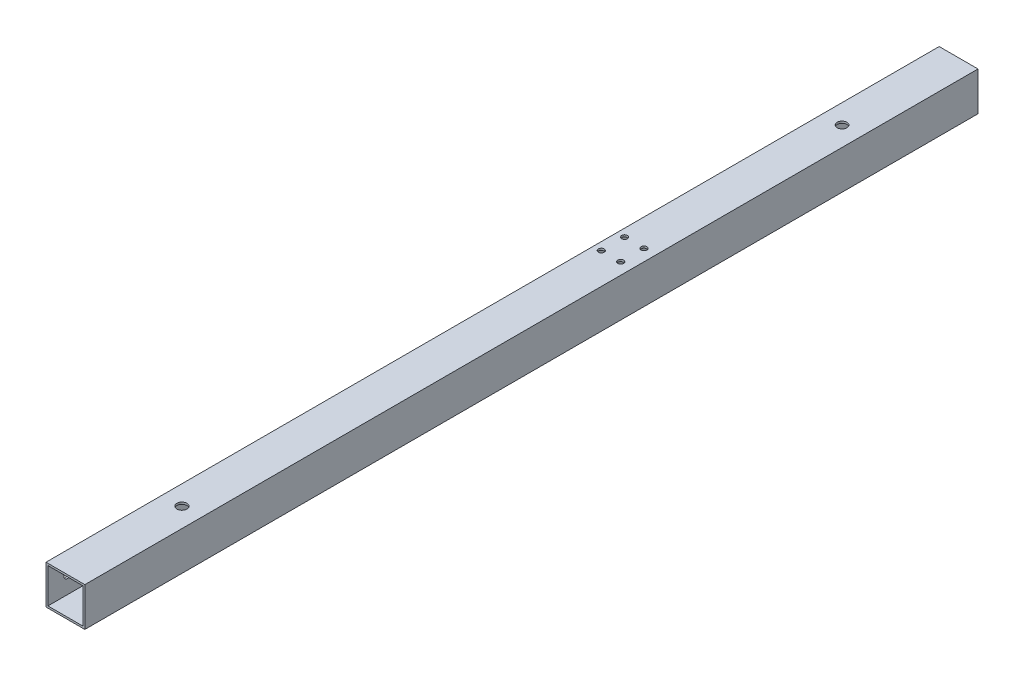
SolidWorks part; units mm, degrees
ref_plane "前视基准面" through (0, 0, 0) normal (0, 0, 1) x (1, 0, 0)
ref_plane "上视基准面" through (0, 0, 0) normal (0, 1, 0) x (1, 0, 0)
ref_plane "右视基准面" through (0, 0, 0) normal (1, 0, 0) x (0, 0, -1)
sketch "草图1" plane through (0, 0, 0) normal (0, 0, 1) x (1, 0, 0)
  line L1 (-10, 10) -> (10, 10)
  line L2 (-10, 10) -> (-10, -10)
  line L3 (-10, -10) -> (10, -10)
  line L4 (10, 10) -> (10, -10)
  line L5 (-10, 10) -> (10, -10) construction
  line L6 (-10, -10) -> (10, 10) construction
  line L7 (-9, 9) -> (9, 9)
  line L8 (-9, 9) -> (-9, -9)
  line L9 (-9, -9) -> (9, -9)
  line L10 (9, 9) -> (9, -9)
  line L11 (-9, 9) -> (9, -9) construction
  line L12 (-9, -9) -> (9, 9) construction
  point P0 (0, 0)
  point P6 (0, 0)
  dimension "D1" = 20
  dimension "D2" = 20
  dimension "D3" = 18
  dimension "D4" = 18
extrude "凸台-拉伸1" add sketch "草图1" along normal blind 460
sketch "草图2" plane through (-10, 0, 0) normal (-1, 0, 0) x (0, 0, 1)
  circle A0 centre (10, 0) radius 1.8
  dimension "D1" = 3.6
extrude "切除-拉伸1" cut sketch "草图2" against normal blind 3
sketch "草图3" plane through (-10, 0, 0) normal (-1, 0, 0) x (0, 0, 1)
  line L1 (0, 10) -> (0, -10) construction
  circle A0 centre (198, 0) radius 1.8
  dimension "D1" = 198
extrude "切除-拉伸2" cut sketch "草图3" against normal blind 3
sketch "草图5" plane through (-10, 0, 0) normal (-1, 0, 0) x (0, 0, 1)
  line L0 (460, 10) -> (460, -10) construction
  circle A0 centre (450, 0) radius 1.8
  dimension "D1" = 10
extrude "切除-拉伸3" cut sketch "草图5" against normal blind 3
sketch "草图6" plane through (-10, 0, 0) normal (-1, 0, 0) x (0, 0, 1)
  line L0 (460, 10) -> (460, -10) construction
  circle A0 centre (262, 0) radius 1.8
  dimension "D1" = 198
extrude "切除-拉伸4" cut sketch "草图6" against normal blind 10
sketch "草图7" plane through (0, 10, 0) normal (0, 1, 0) x (1, 0, 0)
  circle A0 centre (4, -166) radius 1.5
  circle A1 centre (-6, -166) radius 1.5
  circle A2 centre (4, -178) radius 1.5
  circle A3 centre (-6, -178) radius 1.5
extrude "切除-拉伸5" cut sketch "草图7" against normal blind 20
sketch "Sketch1" plane through (0, -10, 0) normal (0, -1, 0) x (1, 0, 0)
  line L0 (-10, 0) -> (10, 0) construction
  circle A0 centre (0, 60) radius 2.5
  dimension "D1" = 5
  dimension "D2" = 60
extrude "Cut-Extrude1" cut sketch "Sketch1" against normal blind 20
sketch "Sketch2" plane through (0, -10, 0) normal (0, -1, 0) x (1, 0, 0)
  line L0 (-10, 460) -> (10, 460) construction
  circle A0 centre (0, 400) radius 2.6
  dimension "D1" = 5.2
  dimension "D2" = 60
extrude "Cut-Extrude2" cut sketch "Sketch2" against normal blind 36
